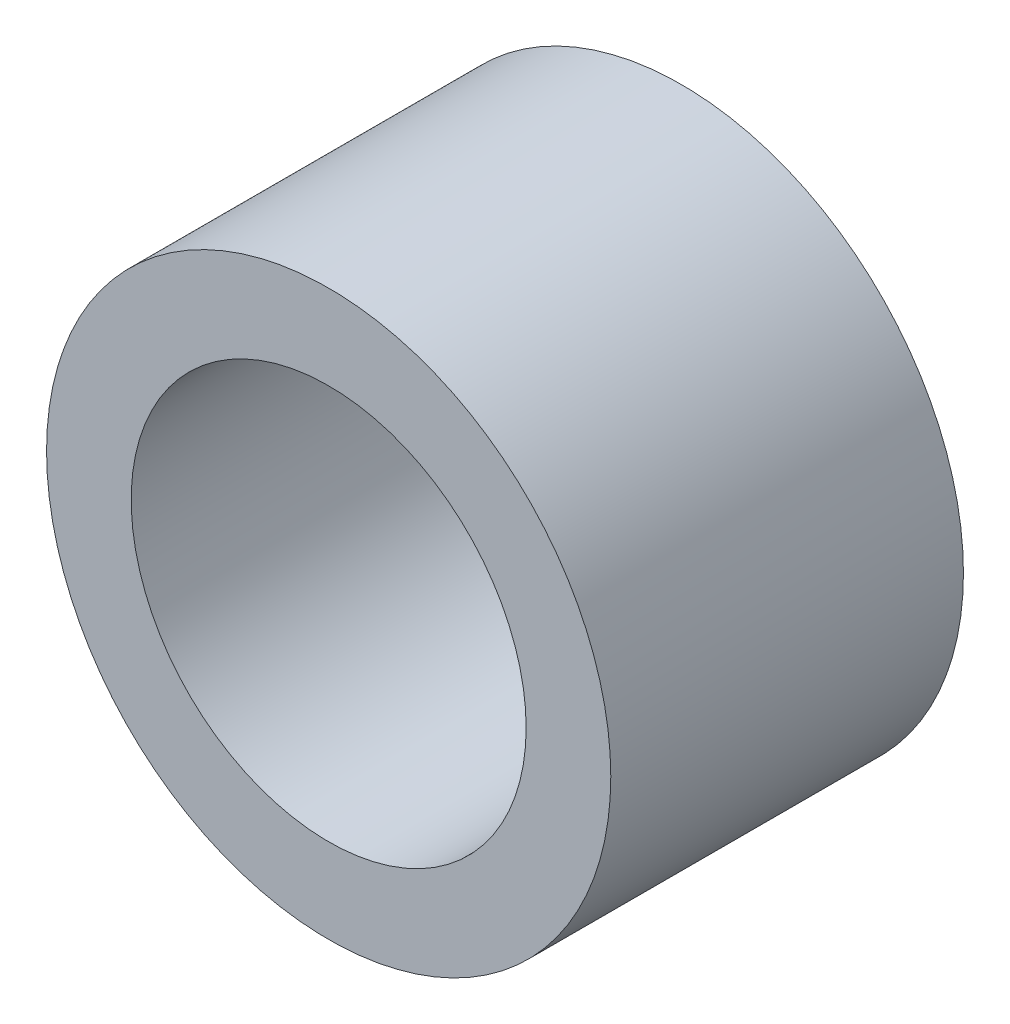
SolidWorks part; units mm, degrees
ref_plane "Front Plane" through (0, 0, 0) normal (0, 0, 1) x (1, 0, 0)
ref_plane "Top Plane" through (0, 0, 0) normal (0, 1, 0) x (1, 0, 0)
ref_plane "Right Plane" through (0, 0, 0) normal (1, 0, 0) x (0, 0, -1)
sketch "Sketch1" plane through (0, 0, 0) normal (0, 0, 1) x (1, 0, 0)
  circle A0 centre (0, 0) radius 5.6
  circle A1 centre (0, 0) radius 8
  dimension "D1" = 11.2
  dimension "D2" = 2.4
extrude "Boss-Extrude1" add sketch "Sketch1" along normal blind 10
